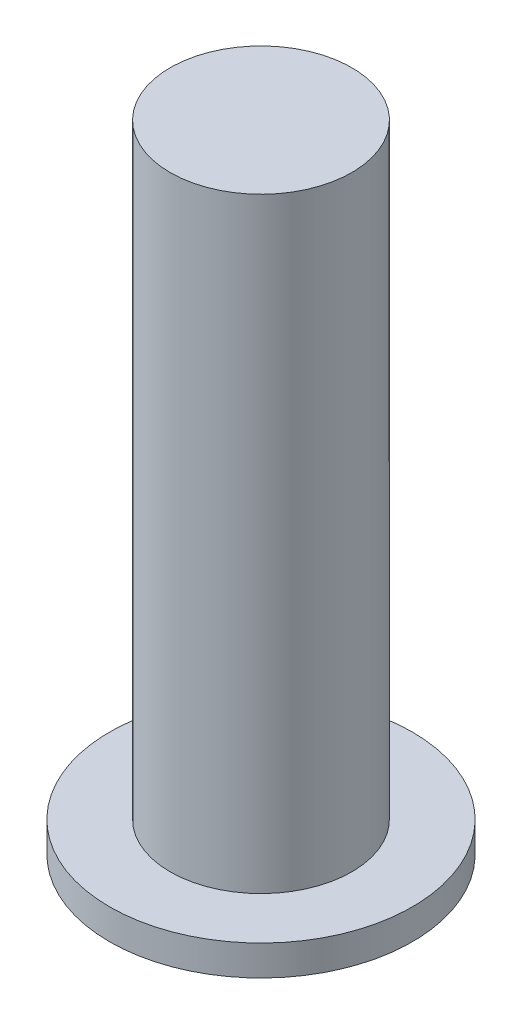
SolidWorks part; units mm, degrees
ref_plane "Front Plane" through (0, 0, 0) normal (0, 0, 1) x (1, 0, 0)
ref_plane "Top Plane" through (0, 0, 0) normal (0, 1, 0) x (1, 0, 0)
ref_plane "Right Plane" through (0, 0, 0) normal (1, 0, 0) x (0, 0, -1)
sketch "Sketch1" plane through (0, 0, 0) normal (0, 1, 0) x (1, 0, 0)
  circle A0 centre (0, 0) radius 50
  point P2 (-253.1593, -104.7131)
  dimension "D1" = 100
extrude "Boss-Extrude1" add sketch "Sketch1" along normal blind 10
sketch "Sketch2" plane through (0, 10, 0) normal (0, 1, 0) x (1, 0, 0)
  circle A0 centre (0, 0) radius 30
  point P3 (-122.4337, -46.4352)
extrude "Boss-Extrude2" add sketch "Sketch2" along normal blind 200
